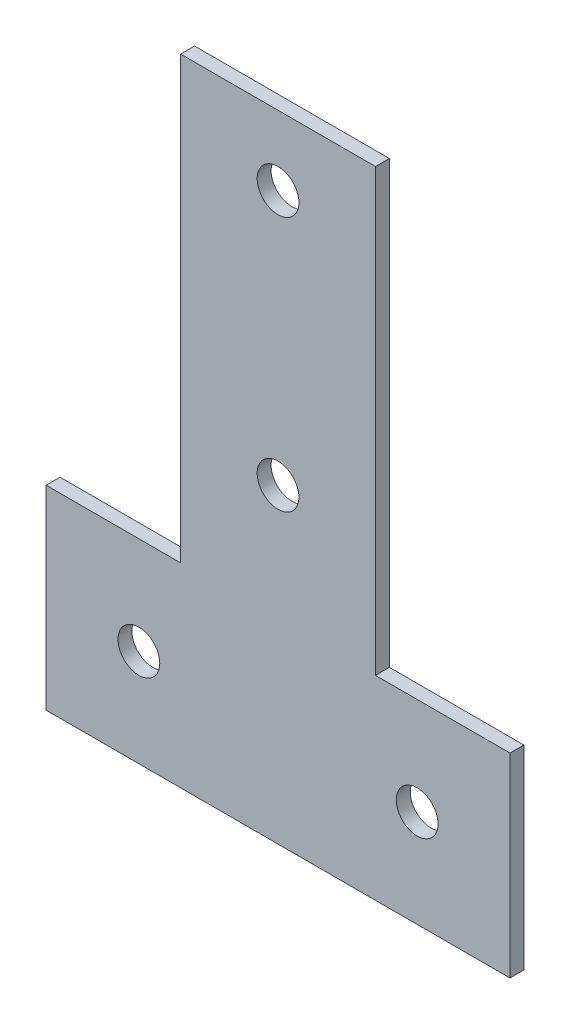
SolidWorks part; units mm, degrees
ref_plane "Спереди" through (0, 0, 0) normal (0, 0, 1) x (1, 0, 0)
ref_plane "Сверху" through (0, 0, 0) normal (0, 1, 0) x (1, 0, 0)
ref_plane "Справа" through (0, 0, 0) normal (1, 0, 0) x (0, 0, -1)
sketch "Эскиз1" plane through (0, 0, 0) normal (0, 0, 1) x (1, 0, 0)
  line L0 (-50, 0) -> (50, 0)
  line L1 (-50, 0) -> (-50, 42)
  line L2 (-50, 42) -> (-21, 42)
  line L3 (-21, 42) -> (-21, 137)
  line L4 (-21, 137) -> (21, 137)
  line L5 (21, 137) -> (21, 42)
  line L6 (21, 42) -> (50, 42)
  line L7 (50, 42) -> (50, 0)
  line L8 (-30, 21) -> (30, 21) construction
  circle A0 centre (0, 122) radius 4.5
  circle A1 centre (0, 67) radius 4.5
  circle A2 centre (-30, 21) radius 4.5
  circle A3 centre (30, 21) radius 4.5
  point P4 (0, 0)
  point P18 (0, 21)
  point P19 (50, 21)
  dimension "D5" = 15
  dimension "D6" = 55
  dimension "D7" = 9
  dimension "D1" = 100
  dimension "D2" = 137
  dimension "D3" = 42
  dimension "D4" = 60
extrude "Бобышка-Вытянуть1" add sketch "Эскиз1" along normal blind 3
